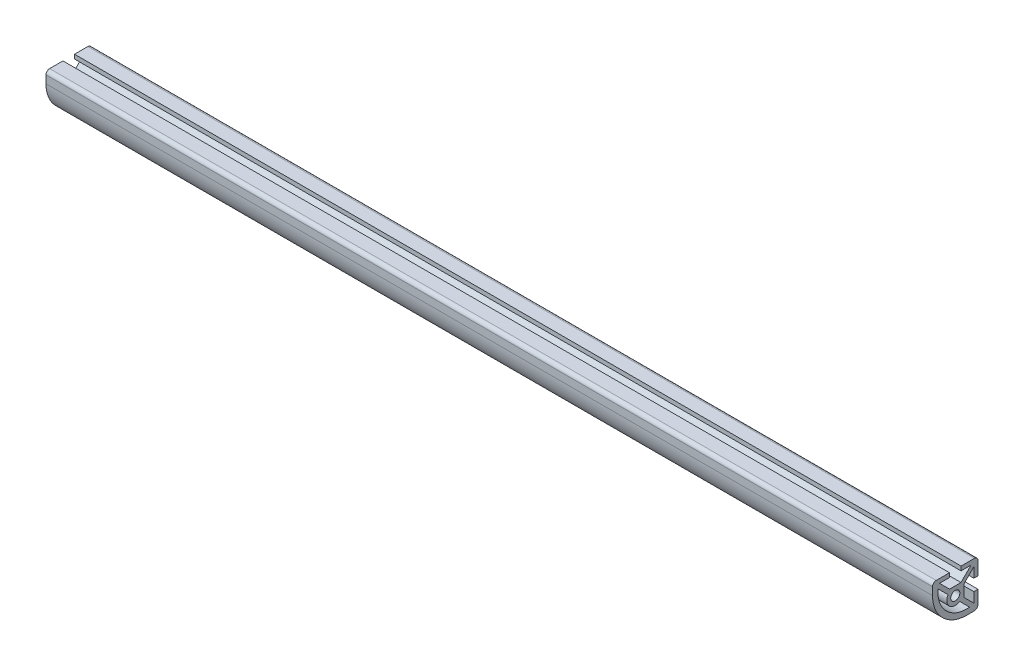
SolidWorks part; units mm, degrees
ref_plane "Front Plane" through (0, 0, 0) normal (0, 0, 1) x (1, 0, 0)
ref_plane "Top Plane" through (0, 0, 0) normal (0, 1, 0) x (1, 0, 0)
ref_plane "Right Plane" through (0, 0, 0) normal (1, 0, 0) x (0, 0, -1)
sketch "Sketch1" plane through (0, 0, 0) normal (1, 0, 0) x (0, 0, -1)
  line L0 (8.0038, -9.5663) -> (2.4852, -4.0478) construction
  line L1 (-4.0478, 2.4852) -> (-9.5663, 8.0038) construction
  line L2 (-3.1872, 4.7498) -> (-8.8006, 10.3632) construction
  line L3 (-8.8006, 10.3632) -> (-3.2385, 10.3632) construction
  line L4 (-3.2385, 10.3632) -> (-3.2385, 12.7) construction
  line L5 (-3.2385, 12.7) -> (-10.668, 12.7) construction
  line L6 (-12.7, 10.668) -> (-12.7, 6.35) construction
  line L7 (6.35, -12.7) -> (10.668, -12.7) construction
  line L8 (12.7, -10.668) -> (12.7, -3.2385) construction
  line L9 (12.7, -3.2385) -> (10.3632, -3.2385) construction
  line L10 (10.3632, -3.2385) -> (10.3632, -8.8006) construction
  line L11 (10.3632, -8.8006) -> (4.7498, -3.1872) construction
  line L12 (4.7498, -3.1872) -> (4.7498, 3.1872) construction
  line L13 (4.7498, 3.1872) -> (10.3632, 8.8006) construction
  line L14 (10.3632, 8.8006) -> (10.3632, 3.2385) construction
  line L15 (10.3632, 3.2385) -> (12.7, 3.2385) construction
  line L16 (12.7, 3.2385) -> (12.7, 10.668) construction
  line L17 (10.668, 12.7) -> (3.2385, 12.7) construction
  line L18 (3.2385, 12.7) -> (3.2385, 10.3632) construction
  line L19 (3.2385, 10.3632) -> (8.8006, 10.3632) construction
  line L20 (8.8006, 10.3632) -> (3.1872, 4.7498) construction
  line L21 (3.1872, 4.7498) -> (-3.1872, 4.7498) construction
  line L22 (-12.7, 0) -> (12.7, 0) construction
  line L23 (0, -12.7) -> (0, 12.7) construction
  line L24 (-7.1204, -7.1204) -> (-4.9651, -4.9651) construction
  line L25 (11.5316, -3.2385) -> (11.5316, 3.2385) construction
  line L26 (-3.2385, 11.5316) -> (3.2385, 11.5316) construction
  line L27 (11.5316, 0) -> (4.7498, 0) construction
  line L28 (0, 11.5316) -> (0, 4.7498) construction
  line L29 (-9.5663, 8.0038) -> (-8.0038, 9.5663) construction
  line L30 (3.1872, 4.7498) -> (4.7498, 3.1872) construction
  circle A0 centre (0, 0) radius 2.5527 construction
  arc A1 (-10.668, 12.7) -> (-12.7, 10.668) centre (-10.668, 10.668) ccw construction
  arc A2 (-12.7, 6.35) -> (6.35, -12.7) centre (6.35, 6.35) ccw construction
  arc A4 (12.7, 10.668) -> (10.668, 12.7) centre (10.668, 10.668) ccw construction
  arc A5 (-4.0478, 2.4852) -> (2.4852, -4.0478) centre (0, 0) ccw construction
  arc A6 (-9.5663, 8.0038) -> (8.0038, -9.5663) centre (6.35, 6.35) ccw construction
  arc A7 (12.7, -10.668) -> (10.668, -12.7) centre (10.668, -10.668) cw construction
  dimension "Radius" = 19.05
  dimension "Corner Radius" = 2.032
  dimension "Center Diameter" = 5.1054
  dimension "Rail Width" = 25.4
  dimension "Outer Thickness" = 2.3368
  dimension "Radius Thickness" = 3.048
  dimension "Leg Thickness" = 2.2098
  dimension "Rail Height" = 25.4
  dimension "TSlot Width" = 6.477
  dimension "TSlot Depth" = 7.9502
sketch "Sketch2" plane through (0, 0, 0) normal (0, 0, 1) x (1, 0, 0)
  line L0 (-247.65, 0) -> (247.65, 0) construction
  point P2 (-196.85, 0)
  point P4 (196.85, 0)
  dimension "Length" = 495.3
  dimension "D1" = 50.8
  dimension "D2" = 50.8
sketch "Sketch3" plane through (0, 0, 0) normal (1, 0, 0) x (0, 0, -1)
  line L0 (-10.668, 12.7) -> (-3.2385, 12.7)
  line L1 (-3.2385, 12.7) -> (-3.2385, 10.3632)
  line L2 (-3.2385, 10.3632) -> (-8.8006, 10.3632)
  line L3 (-8.8006, 10.3632) -> (-3.1872, 4.7498)
  line L4 (-3.1872, 4.7498) -> (3.1872, 4.7498)
  line L5 (3.1872, 4.7498) -> (8.8006, 10.3632)
  line L6 (8.8006, 10.3632) -> (3.2385, 10.3632)
  line L7 (3.2385, 10.3632) -> (3.2385, 12.7)
  line L8 (3.2385, 12.7) -> (10.668, 12.7)
  line L9 (12.7, 10.668) -> (12.7, 3.2385)
  line L10 (12.7, 3.2385) -> (10.3632, 3.2385)
  line L11 (10.3632, 3.2385) -> (10.3632, 8.8006)
  line L12 (10.3632, 8.8006) -> (4.7498, 3.1872)
  line L13 (4.7498, 3.1872) -> (4.7498, -3.1872)
  line L14 (4.7498, -3.1872) -> (10.3632, -8.8006)
  line L15 (10.3632, -8.8006) -> (10.3632, -3.2385)
  line L16 (10.3632, -3.2385) -> (12.7, -3.2385)
  line L17 (12.7, -3.2385) -> (12.7, -10.668)
  line L18 (2.4852, -4.0478) -> (8.0038, -9.5663)
  line L19 (10.668, -12.7) -> (6.35, -12.7)
  line L20 (-9.5663, 8.0038) -> (-4.0478, 2.4852)
  line L21 (-12.7, 10.668) -> (-12.7, 6.35)
  arc A0 (-12.7, 10.668) -> (-10.668, 12.7) centre (-10.668, 10.668) cw
  arc A1 (10.668, 12.7) -> (12.7, 10.668) centre (10.668, 10.668) cw
  arc A2 (12.7, -10.668) -> (10.668, -12.7) centre (10.668, -10.668) cw
  arc A3 (-12.7, 6.35) -> (6.35, -12.7) centre (6.35, 6.35) ccw
  arc A4 (-4.0478, 2.4852) -> (2.4852, -4.0478) centre (0, 0) ccw
  arc A7 (-4.0478, 2.4852) -> (2.4852, -4.0478) centre (0, 0) ccw construction
  arc A8 (-9.5663, 8.0038) -> (8.0038, -9.5663) centre (6.35, 6.35) ccw
  circle A9 centre (0, 0) radius 2.5527
  circle A10 centre (0, 0) radius 2.5527 construction
extrude "Boss-Extrude1" add sketch "Sketch3" along normal up to vertex (247.65 mm away) and the other way up to vertex (247.65 mm away) up to point (247.65, 0, 0) other way up to point (-247.65, 0, 0)
equation "\"D1@Sketch2\"=\"Rail Width@Sketch1\"*2"
equation "\"D2@Sketch2\"=\"D1@Sketch2\""
